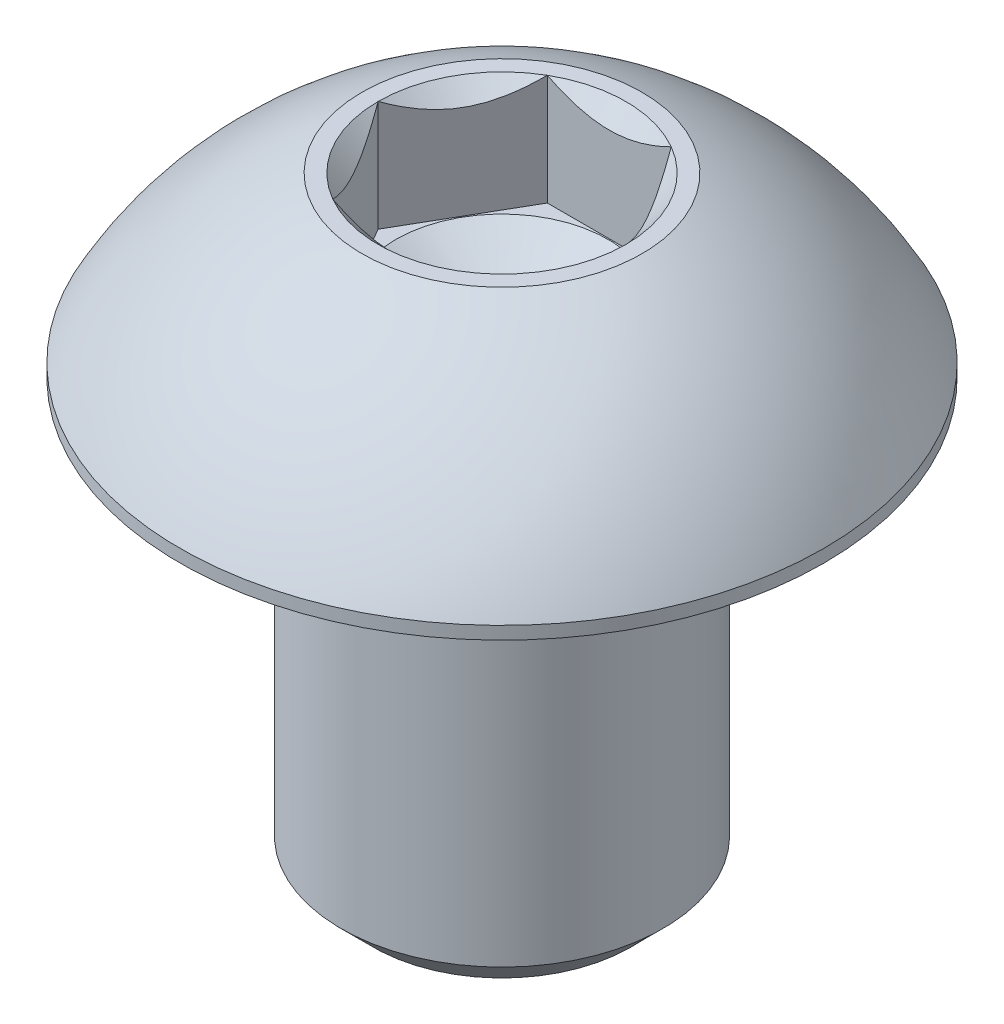
SolidWorks part; units mm, degrees
material "1.0570 (St52)"
ref_plane "vorne" through (0, 0, 0) normal (0, 0, 1) x (1, 0, 0)
ref_plane "oben" through (0, 0, 0) normal (0, 1, 0) x (1, 0, 0)
ref_plane "rechts" through (0, 0, 0) normal (1, 0, 0) x (0, 0, -1)
sketch "Skizze1" plane through (0, 0, 0) normal (0, 0, -1) x (1, 0, 0)
  line L0 (0, 11.3) -> (2.4, 11.3)
  line L1 (2.4, 11.3) -> (3, 10.7)
  line L2 (3, 3.3) -> (3, 10.7)
  line L3 (3, 3.3) -> (6, 3.3)
  line L7 (2.6094, 0) -> (2.3094, 0)
  line L8 (2.3094, 0) -> (1.98, 0.3294)
  line L9 (1.98, 0.3294) -> (1.98, 2.0625)
  line L10 (1.98, 2.0625) -> (0, 3.2522)
  line L11 (0, 3.2522) -> (0, 11.3)
  line L12 (0, 0) -> (0, 11.3) construction
  line L13 (6, 3.3) -> (6, 3.0614)
  arc A1 (2.6094, 0) -> (6, 3.0614) centre (0, 6.2983) ccw
revolve "Rotation1" add sketch "Skizze1" angle 360 about L12
sketch "Skizze2" plane through (1.9736, 0, -1.4688) normal (0, 1, 0) x (-1, 0, 0)
  line L0 (0.8189, -0.5312) -> (3.1283, -0.5312)
  line L1 (3.1283, -0.5312) -> (4.283, 1.4688)
  line L2 (3.1283, 3.4688) -> (4.283, 1.4688)
  line L3 (0.8189, 3.4688) -> (3.1283, 3.4688)
  line L4 (0.8189, 3.4688) -> (-0.3358, 1.4688)
  line L5 (0.8189, -0.5312) -> (-0.3358, 1.4688)
  line L6 (1.9736, 3.4688) -> (1.9736, -0.5312) construction
  line L7 (-0.3358, 1.4688) -> (4.283, 1.4688) construction
  point P3 (1.9736, 3.4688)
  point P5 (1.9736, -0.5312)
  point P10 (1.9736, 1.4688)
  dimension "D1" = 120
  dimension "S" = 4
extrude "Schnitt-Linear austragen1" cut sketch "Skizze2" against normal blind 2.0625
equation "\"Anplanung und zyl. Kopf@Skizze1\" = \"DG@Skizze1\" * 0.05"
